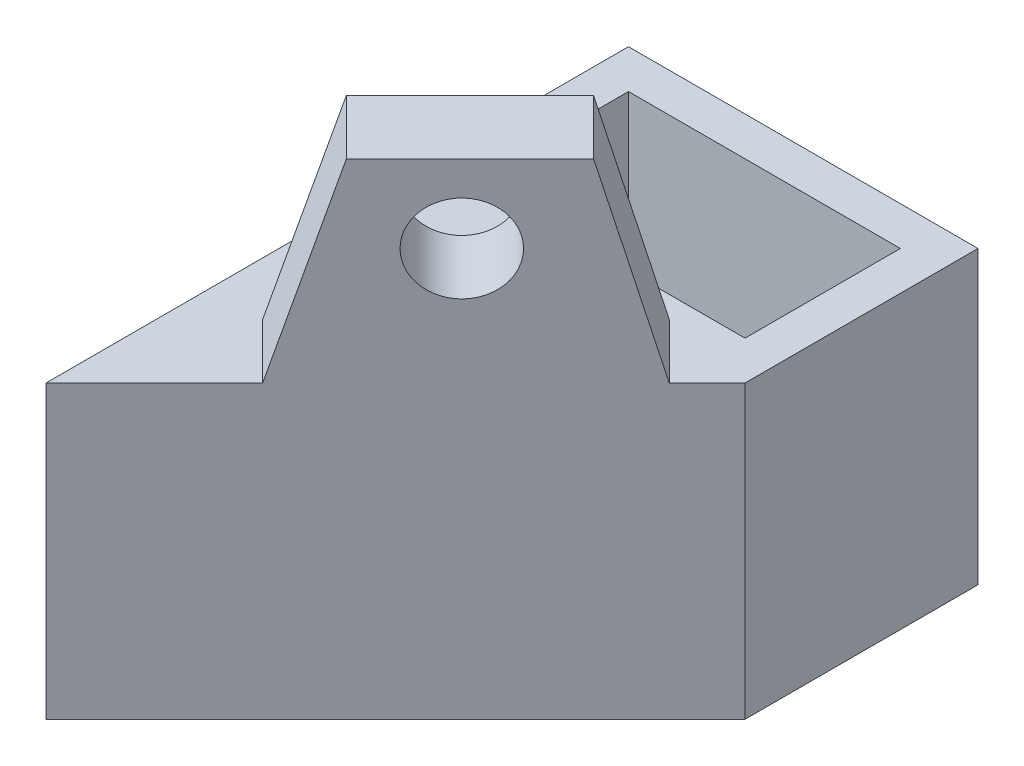
SolidWorks part; units mm, degrees
ref_plane "前视基准面" through (0, 0, 0) normal (0, 0, 1) x (1, 0, 0)
ref_plane "上视基准面" through (0, 0, 0) normal (0, 1, 0) x (1, 0, 0)
ref_plane "右视基准面" through (0, 0, 0) normal (1, 0, 0) x (0, 0, -1)
sketch "草图1" plane through (0, 0, 0) normal (0, 1, 0) x (1, 0, 0)
  line L0 (0, 0) -> (0, 10)
  line L1 (0, 10) -> (18, 10)
  line L2 (18, 10) -> (18, -2)
  line L3 (18, -2) -> (0, -20)
  line L4 (0, -20) -> (0, 0)
  line L6 (2, 8) -> (16, 8)
  line L7 (2, 8) -> (2, 0)
  line L8 (2, 0) -> (16, 0)
  line L9 (16, 8) -> (16, 0)
extrude "凸台-拉伸1" add sketch "草图1" along normal blind 15
sketch "草图2" plane through (0, 15, 0) normal (0, 1, 0) x (1, 0, 0)
  line L0 (11.2722, -3.0709) -> (14.1006, -5.8994)
  line L1 (4.9063, -9.4368) -> (7.7347, -12.2653)
  line L4 (7.7347, -12.2653) -> (14.1006, -5.8994)
  line L5 (4.9063, -9.4368) -> (11.2722, -3.0709)
extrude "凸台-拉伸2" add sketch "草图2" along normal blind 10
sketch "草图4" plane through (7.1716, 0, 7.1716) normal (-0.7071, 0, -0.7071) x (-0.7071, 0, 0.7071)
  circle A0 centre (-1, 21) radius 2.25
extrude "切除-拉伸1" cut sketch "草图4" against normal blind 5.5
sketch "草图5" plane through (10, 0, 10) normal (0.7071, 0, 0.7071) x (0.7071, 0, -0.7071)
  line L0 (5.7992, 25) -> (5.7992, 15)
  line L1 (5.7992, 15) -> (8.5564, 15)
  line L3 (8.5564, 15) -> (5.7992, 25)
  line L5 (-3.2036, 25) -> (-3.2036, 15)
  line L6 (-3.2036, 15) -> (-6.2534, 15)
  line L8 (-6.2534, 15) -> (-3.2036, 25)
extrude "凸台-拉伸3" add sketch "草图5" against normal blind 4
